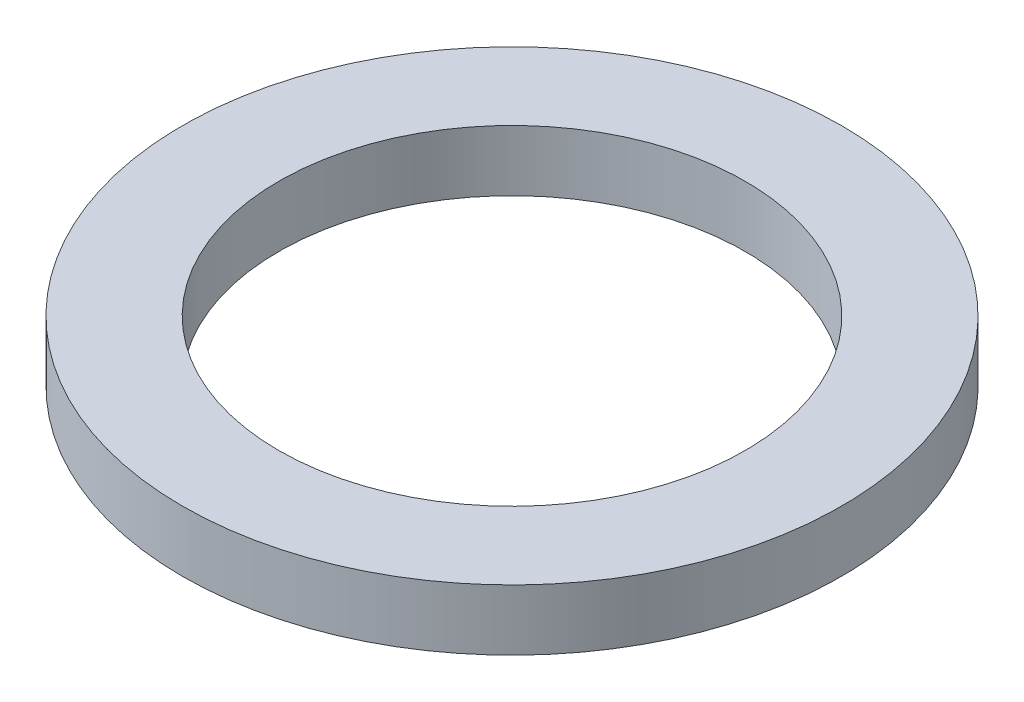
SolidWorks part; units mm, degrees
material "1023 Chapa de acero al carbono (SS)"
ref_plane "Alzado" through (0, 0, 0) normal (0, 0, 1) x (1, 0, 0)
ref_plane "Planta" through (0, 0, 0) normal (0, 1, 0) x (1, 0, 0)
ref_plane "Vista lateral" through (0, 0, 0) normal (1, 0, 0) x (0, 0, -1)
sketch "Sketch1" plane through (0, 0, 0) normal (0, 1, 0) x (1, 0, 0)
  circle A0 centre (0, 0) radius 32.5
  circle A1 centre (0, 0) radius 23
  dimension "D1" = 46
  dimension "D2" = 65
extrude "Extrude1" add sketch "Sketch1" along normal blind 6
